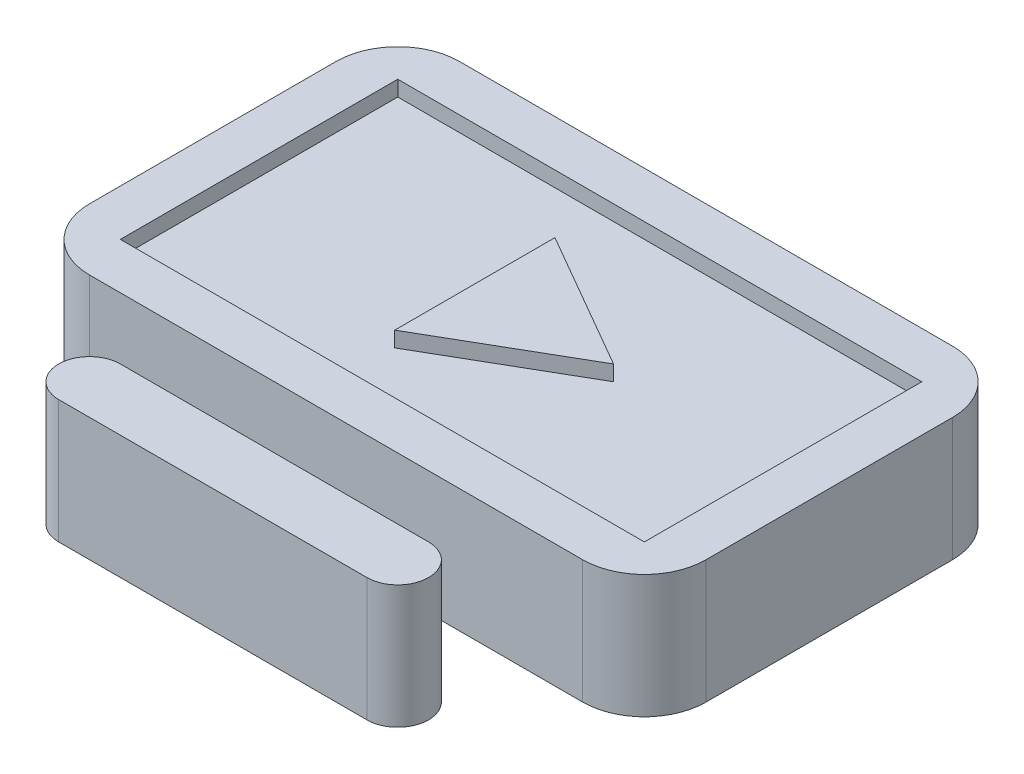
SolidWorks part; units mm, degrees
material "6061-T4 (SS)"
ref_plane "Front" through (0, 0, 0) normal (0, 0, 1) x (1, 0, 0)
ref_plane "Top" through (0, 0, 0) normal (0, 1, 0) x (1, 0, 0)
ref_plane "Right" through (0, 0, 0) normal (1, 0, 0) x (0, 0, -1)
sketch "Sketch2" plane through (0, 0, 0) normal (0, 1, 0) x (1, 0, 0)
  line L0 (-63.5, 0) -> (63.5, 0) construction
  line L1 (-63.5, 12.7) -> (63.5, 12.7)
  line L2 (-63.5, -12.7) -> (63.5, -12.7)
  line L3 (0, 0) -> (0, 38.1) construction
  line L4 (12.7, 0) -> (12.7, 38.1)
  line L5 (-12.7, 0) -> (-12.7, 38.1)
  line L6 (-12.7, 0) -> (-12.7, 38.1) construction
  line L7 (-127, 190.5) -> (127, 190.5)
  line L8 (-127, 190.5) -> (-127, 38.1)
  line L9 (-127, 38.1) -> (127, 38.1)
  line L10 (127, 190.5) -> (127, 38.1)
  line L11 (-127, 190.5) -> (127, 38.1) construction
  line L12 (-127, 38.1) -> (127, 190.5) construction
  arc A0 (-63.5, 12.7) -> (-63.5, -12.7) centre (-63.5, 0) ccw
  arc A1 (63.5, -12.7) -> (63.5, 12.7) centre (63.5, 0) ccw
  point P2 (0, 0)
  point P14 (0, 114.3)
  dimension "D1" = 25.4
  dimension "D2" = 127
  dimension "D5" = 254
  dimension "D6" = 152.4
  dimension "D7" = 25.4
  dimension "D3" = 12.7
  dimension "D4" = 12.7
extrude "Boss-Extrude1" add sketch "Sketch2" along normal blind 50.8
fillet "Fillet1" radius 25.4 4 edges at (127, 25.4, -38.1) (-127, 25.4, -38.1) (-127, 25.4, -190.5) (127, 25.4, -190.5)
sketch "Sketch4" plane through (0, 50.8, 0) normal (0, 1, 0) x (1, 0, 0)
  line L0 (-127, 114.3) -> (127, 114.3) construction
  line L1 (-127, 165.1) -> (-127, 63.5) construction
  line L2 (127, 165.1) -> (127, 63.5) construction
  line L3 (-101.6, 190.5) -> (101.6, 190.5) construction
  line L4 (-107.95, 57.15) -> (107.95, 57.15)
  line L5 (-107.95, 57.15) -> (-107.95, 171.45)
  line L6 (-107.95, 171.45) -> (107.95, 171.45)
  line L7 (107.95, 57.15) -> (107.95, 171.45)
  line L8 (-107.95, 57.15) -> (107.95, 171.45) construction
  line L9 (-107.95, 171.45) -> (107.95, 57.15) construction
  point P6 (0, 114.3)
  dimension "D1" = 19.05
  dimension "D2" = 19.05
extrude "Cut-Extrude1" cut sketch "Sketch4" against normal blind 6.35
sketch "Sketch5" plane through (0, 44.45, 0) normal (0, 1, 0) x (1, 0, 0)
  line L0 (0, 171.45) -> (0, 57.15) construction
  line L1 (107.95, 171.45) -> (-107.95, 171.45) construction
  line L2 (-107.95, 57.15) -> (107.95, 57.15) construction
  line L4 (38.1, 114.3) -> (-19.05, 147.2956)
  line L5 (-19.05, 147.2956) -> (-19.05, 81.3044)
  line L6 (-19.05, 81.3044) -> (38.1, 114.3)
  circle A0 centre (0, 114.3) radius 19.05 construction
  dimension "D1" = 38.1
extrude "Boss-Extrude2" add sketch "Sketch5" along normal up to surface (6.35 mm away) up to face at (0, 50.8, -114.3)
sketch "Sketch6" plane through (0, 50.8, 0) normal (0, 1, 0) x (1, 0, 0)
  line L1 (-12.7, 38.1) -> (12.7, 38.1)
  line L2 (-12.7, 38.1) -> (-12.7, 12.7)
  line L3 (-12.7, 12.7) -> (12.7, 12.7)
  line L4 (12.7, 38.1) -> (12.7, 12.7)
extrude "Cut-Extrude2" cut sketch "Sketch6" against normal blind 25.4
equation "\"D2@Sketch4\"=\"D1@Sketch4\""
